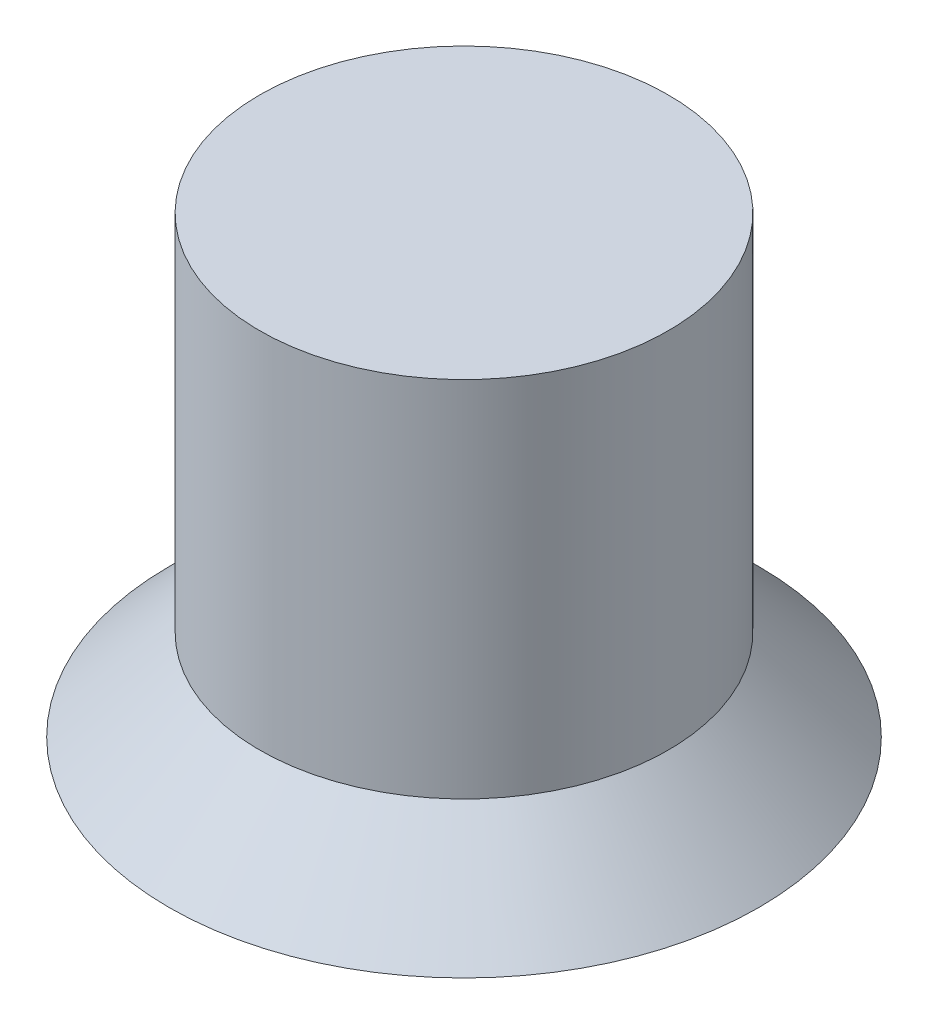
SolidWorks part; units mm, degrees
ref_plane "Front Plane" through (0, 0, 0) normal (0, 0, 1) x (1, 0, 0)
ref_plane "Top Plane" through (0, 0, 0) normal (0, 1, 0) x (1, 0, 0)
ref_plane "Right Plane" through (0, 0, 0) normal (1, 0, 0) x (0, 0, -1)
sketch "Sketch1" plane through (0, 0, 0) normal (0, 0, 1) x (1, 0, 0)
  line L6 (0, 0) -> (6.5, 0)
  line L7 (6.5, 0) -> (4.5, 2)
  line L8 (4.5, 2) -> (4.5, 10)
  line L9 (4.5, 10) -> (0, 10)
  line L10 (0, 10) -> (0, 0)
  dimension "D1" = 6.5
  dimension "D2" = 4.5
  dimension "D3" = 45
  dimension "D4" = 10
revolve "Revolve1" add sketch "Sketch1" angle 360 about L10
sketch "Sketch2" plane through (0, 0, 0) normal (0, -1, 0) x (1, 0, 0)
  circle A0 centre (4, 0) radius 1.5
  dimension "D1" = 3
  dimension "D2" = 4
extrude "Boss-Extrude1" add sketch "Sketch2" along normal blind 0.5
fillet "Fillet1" radius 0.3 1 edges at (5.5, -0.5, 0)
